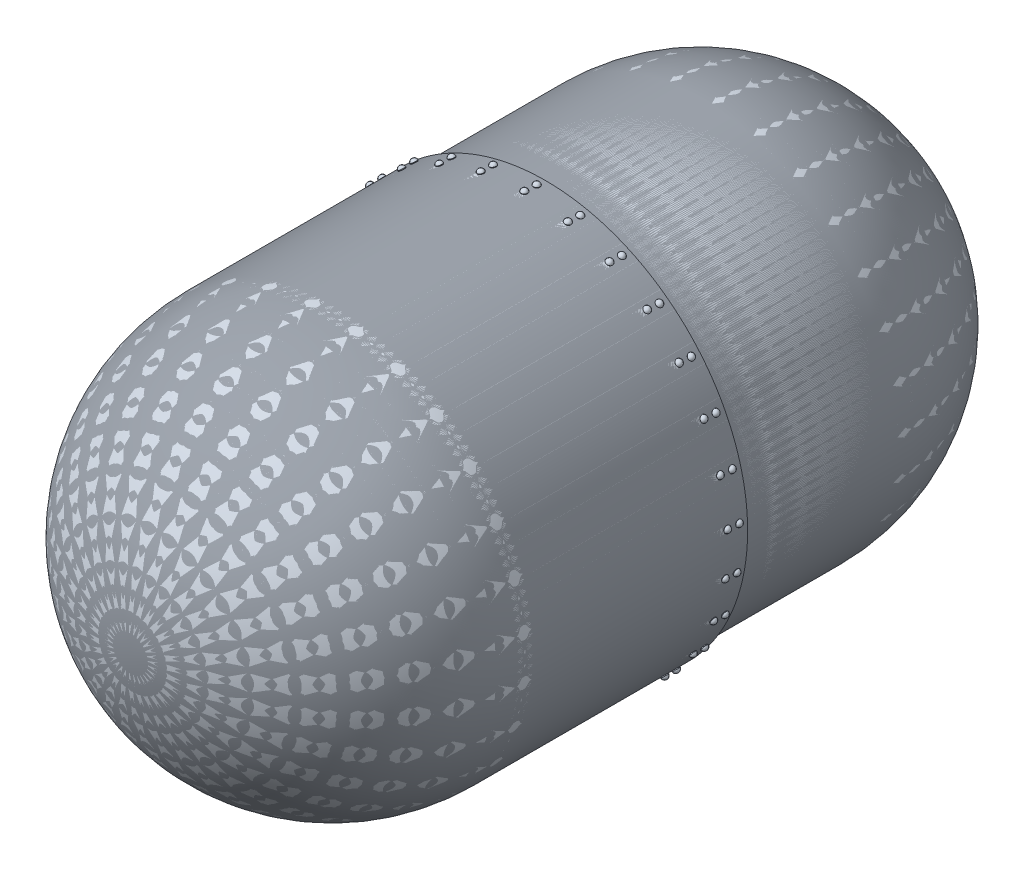
SolidWorks part; units mm, degrees
ref_plane "Front Plane" through (0, 0, 0) normal (0, 0, 1) x (1, 0, 0)
ref_plane "Top Plane" through (0, 0, 0) normal (0, 1, 0) x (1, 0, 0)
ref_plane "Right Plane" through (0, 0, 0) normal (1, 0, 0) x (0, 0, -1)
sketch "Sketch1" plane through (0, 0, 0) normal (0, 0, 1) x (1, 0, 0)
  circle A0 centre (0, 0) radius 1200
  circle A1 centre (0, 0) radius 1165
  dimension "D" = 2400
  dimension "t" = 35
extrude "Boss-Extrude1" add sketch "Sketch1" along normal blind 1126
sketch "Sketch2" plane through (0, 0, 1126) normal (0, 0, 1) x (1, 0, 0)
  circle A0 centre (0, 0) radius 1235
  circle A1 centre (0, 0) radius 1200
  dimension "D" = 2400
  dimension "t" = 35
extrude "Boss-Extrude2" add sketch "Sketch2" along normal blind 1126 and the other way blind 180
ref_plane "Plane1" through (0, 0, 946) normal (0, 0, -1) x (-1, 0, 0)
ref_plane "Plane3" through (0, 0, 1000) normal (0, 0, -1) x (-1, 0, 0)
sketch "Sketch7" plane through (0, 0, 1000) normal (0, 0, -1) x (-1, 0, 0)
  line L0 (0, 0) -> (0, 1764.1602) construction
  line L1 (0, 1235) -> (18, 1235)
  line L2 (18, 1235) -> (20.5981, 1239.5)
  line L3 (20.5981, 1239.5) -> (0, 1239.5)
  line L4 (0, 1239.5) -> (0, 1235)
  circle A0 centre (0, 0) radius 1235 construction
  point P3 (0, 1235)
  dimension "rvt_rad" = 18
  dimension "rvt_taper_angle" = 120
  dimension "rvt_taper_height" = 4.5
revolve "Revolve1" add sketch "Sketch7" angle 360 about L0
sketch "Sketch8" plane through (0, 0, 1000) normal (0, 0, -1) x (-1, 0, 0)
  line L0 (-18.5196, 1235.9) -> (18.5196, 1235.9) construction
  line L1 (18, 1235) -> (20.5981, 1239.5) construction
  line L2 (18, 1235) -> (20.5981, 1239.5) construction
  line L3 (-20.5981, 1239.5) -> (-18, 1235) construction
  line L4 (0, 1050.2902) -> (0, 1087.9986) construction
  line L5 (20.5981, 1239.5) -> (-20.5981, 1239.5) construction
  line L6 (0, 1256.8103) -> (0, 1239.5)
  line L7 (0, 1239.5) -> (20.5981, 1239.5)
  arc A0 (20.5981, 1239.5) -> (0, 1256.8103) centre (0, 1235.9) ccw
  point P0 (0, 1235.9)
  point P6 (0, 1235.9)
  dimension "arc_center_dist" = 3.6
revolve "Revolve2" add sketch "Sketch8" angle 360 about L6
pattern_circular "CirPattern1" count 29 over 360 about axis through (0, 0, 946) along (0, 0, 1) of bodies 104
sketch "Sketch9" plane through (0, 0, 0) normal (0, 1, 0) x (1, 0, 0)
  line L0 (0, 0) -> (1200, 0)
  line L1 (0, 1200) -> (0, 0)
  arc A0 (1200, 0) -> (0, 1200) centre (0, 0) ccw
revolve "Revolve3" add sketch "Sketch9" angle 360 about L1
sketch "Sketch10" plane through (0, 0, 0) normal (0, 1, 0) x (1, 0, 0)
  line L0 (0, -2252) -> (1235, -2252)
  line L1 (-1235, -2252) -> (1235, -2252) construction
  line L2 (0, -2252) -> (0, -3487)
  arc A0 (1235, -2252) -> (0, -3487) centre (0, -2252) cw
revolve "Revolve4" add sketch "Sketch10" angle 360 about L2
ref_plane "Plane4" through (0, 0, 1072) normal (0, 0, -1) x (-1, 0, 0)
sketch "Sketch11" plane through (0, 0, 1072) normal (0, 0, -1) x (-1, 0, 0)
  line L0 (0, 0) -> (0, 1427.9587) construction
  line L1 (0, 0) -> (-305.3886, 1406.7903) construction
  line L2 (-261.9662, 1206.7621) -> (-244.3759, 1210.5806)
  line L3 (-244.3759, 1210.5806) -> (-242.7915, 1215.5294)
  line L4 (-242.7915, 1215.5294) -> (-262.9208, 1211.1597)
  line L5 (-262.9208, 1211.1597) -> (-261.9662, 1206.7621)
  circle A1 centre (0, 0) radius 1235 construction
  point P3 (-261.994, 1206.8903)
  point P8 (0, 1235)
  dimension "rvt_rad" = 18
  dimension "taper_angle" = 120
  dimension "taper_height" = 4.5
  dimension "dist_to_decide_diagonal_pitch" = 264
revolve "Revolve5" add sketch "Sketch11" angle 360 about L5
sketch "Sketch12" plane through (0, 0, 1072) normal (0, 0, -1) x (-1, 0, 0)
  line L0 (-262.9208, 1211.1597) -> (-261.9662, 1206.7621) construction
  line L1 (-242.7915, 1215.5294) -> (-283.05, 1206.79) construction
  line L2 (0, 0) -> (-305.3886, 1406.7903) construction
  line L3 (-266.593, 1228.076) -> (-262.9208, 1211.1597)
  line L4 (-262.9208, 1211.1597) -> (-242.7915, 1215.5294)
  arc A0 (-242.7915, 1215.5294) -> (-266.593, 1228.076) centre (-262.1571, 1207.6416) ccw
  point P0 (-262.1571, 1207.6416)
  dimension "arc_center_dist" = 3.6
revolve "Revolve6" add sketch "Sketch12" angle 360 about L3
pattern_circular "CirPattern2" count 29 over 360 about axis through (0, 0, 946) along (0, 0, 1) of bodies 158
